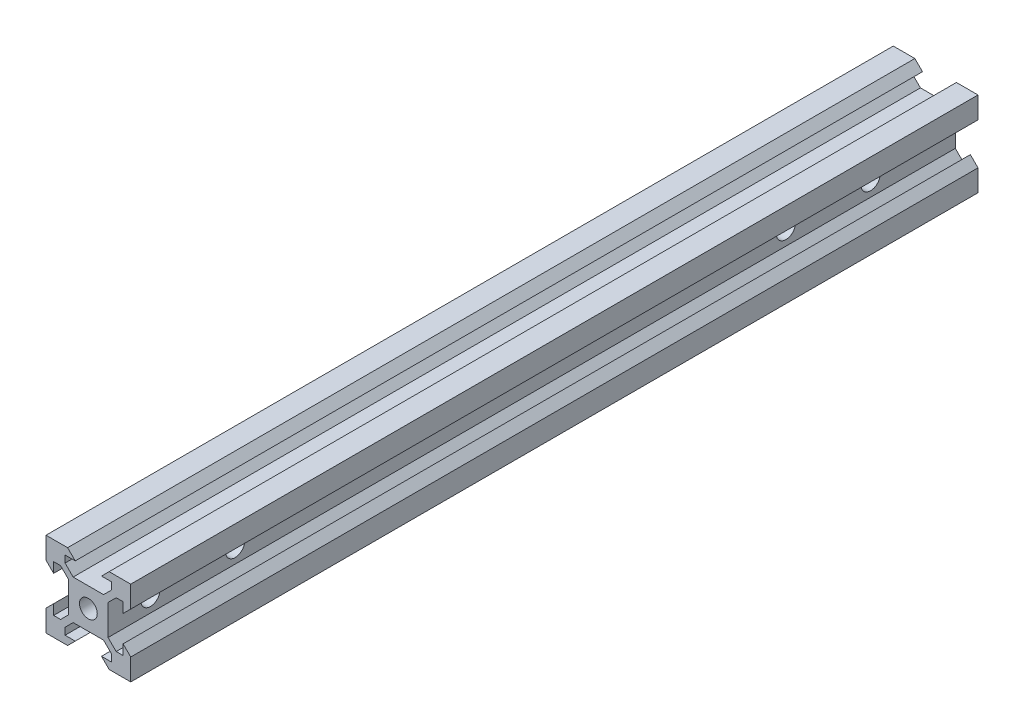
SolidWorks part; units mm, degrees
material "6063-T5"
ref_plane "Front Plane" through (0, 0, 0) normal (0, 0, 1) x (1, 0, 0)
ref_plane "Top Plane" through (0, 0, 0) normal (0, 1, 0) x (1, 0, 0)
ref_plane "Right Plane" through (0, 0, 0) normal (1, 0, 0) x (0, 0, -1)
sketch "Sketch1" plane through (0, 0, 0) normal (0, 0, 1) x (1, 0, 0)
  line L0 (3.59, 4.6507) -> (-3.59, 4.6507)
  line L5 (-10, -10) -> (10, -10)
  line L6 (-10, -10) -> (-10, 10)
  line L7 (-10, 10) -> (10, 10)
  line L8 (10, -10) -> (10, 10)
  line L9 (-10, -10) -> (10, 10) construction
  line L10 (-10, 10) -> (10, -10) construction
  line L11 (0, 10) -> (0, -10) construction
  line L12 (10, 0) -> (-10, 0) construction
  line L13 (-3.59, 4.6507) -> (-5.4993, 6.56)
  line L14 (-5.4993, 6.56) -> (-5.4993, 8.2)
  line L15 (3.59, 4.6507) -> (5.4993, 6.56)
  line L16 (5.4993, 6.56) -> (5.4993, 8.2)
  line L17 (5.4993, 8.2) -> (3.1, 8.2)
  line L18 (3.1, 8.2) -> (4.9, 10)
  line L19 (-5.4993, 8.2) -> (-3.1, 8.2)
  line L20 (-3.1, 8.2) -> (-4.9, 10)
  line L21 (3.1, -8.2) -> (4.9, -10)
  line L22 (5.4993, -8.2) -> (3.1, -8.2)
  line L23 (5.4993, -6.56) -> (5.4993, -8.2)
  line L24 (3.59, -4.6507) -> (5.4993, -6.56)
  line L25 (3.59, -4.6507) -> (-3.59, -4.6507)
  line L26 (-3.59, -4.6507) -> (-5.4993, -6.56)
  line L27 (-5.4993, -6.56) -> (-5.4993, -8.2)
  line L28 (-5.4993, -8.2) -> (-3.1, -8.2)
  line L29 (-3.1, -8.2) -> (-4.9, -10)
  line L30 (8.2, 3.1) -> (10, 4.9)
  line L31 (8.2, 3.1) -> (8.2, 5.4993)
  line L32 (8.2, 5.4993) -> (6.56, 5.4993)
  line L33 (4.6507, 3.59) -> (6.56, 5.4993)
  line L34 (4.6507, 3.59) -> (4.6507, -3.59)
  line L35 (4.6507, -3.59) -> (6.56, -5.4993)
  line L36 (8.2, -5.4993) -> (6.56, -5.4993)
  line L37 (8.2, -3.1) -> (8.2, -5.4993)
  line L38 (8.2, -3.1) -> (10, -4.9)
  line L39 (-8.2, -3.1) -> (-10, -4.9)
  line L40 (-8.2, -3.1) -> (-8.2, -5.4993)
  line L41 (-8.2, -5.4993) -> (-6.56, -5.4993)
  line L42 (-4.6507, -3.59) -> (-6.56, -5.4993)
  line L43 (-4.6507, 3.59) -> (-4.6507, -3.59)
  line L44 (-4.6507, 3.59) -> (-6.56, 5.4993)
  line L45 (-8.2, 5.4993) -> (-6.56, 5.4993)
  line L46 (-8.2, 3.1) -> (-8.2, 5.4993)
  line L47 (-8.2, 3.1) -> (-10, 4.9)
  line L48 (4.9, 10) -> (-4.9, 10)
  line L49 (-10, 4.9) -> (-10, -4.9)
  line L50 (10, -4.9) -> (10, 4.9)
  line L51 (4.9, -10) -> (-4.9, -10)
  circle A1 centre (0, 0) radius 2.1
  point P11 (0, 4.6507)
  point P35 (4.6507, 0)
  dimension "D1" = 4.2
  dimension "D2" = 20
  dimension "D3" = 20
  dimension "D4" = 0.75
  dimension "D5" = 3.59
  dimension "D6" = 3.1
  dimension "D7" = 1.8
  dimension "D8" = 1.64
  dimension "D9" = 3.59
  dimension "D10" = 1.64
  dimension "D11" = 1.8
  dimension "D12" = 45
  dimension "D13" = 0.75
  dimension "D14" = 3.1
extrude "Boss-Extrude1" add sketch "Sketch1" along normal mid plane 200 contours L6 L5 L8 L7 | A1 | L50 L30 L31 L32 L33 L34 L35 L36 L37 L38 | L48 L20 L19 L14 L13 L0 L15 L16 L17 L18 | L49 L39 L40 L41 L42 L43 L44 L45 L46 L47 | L51 L29 L28 L27 L26 L25 L24 L23 L22 L21
sketch "Sketch3" plane through (4.6507, 0, 0) normal (1, 0, 0) x (0, 0, -1)
  line L0 (-100, 0) -> (100, 0) construction
  line L1 (-100, 3.59) -> (-100, -3.59) construction
  line L2 (100, 3.59) -> (100, -3.59) construction
  circle A0 centre (-90, 0) radius 2.25
  circle A1 centre (-70, 0) radius 2.25
  circle A2 centre (60, 0) radius 2.25
  circle A3 centre (80, 0) radius 2.25
  dimension "D1" = 4.5
  dimension "D2" = 10
  dimension "D4" = 20
  dimension "D6" = 150
  dimension "D3" = 2
  dimension "D5" = 2
extrude "Cut-Extrude1" cut sketch "Sketch3" against normal up to next
